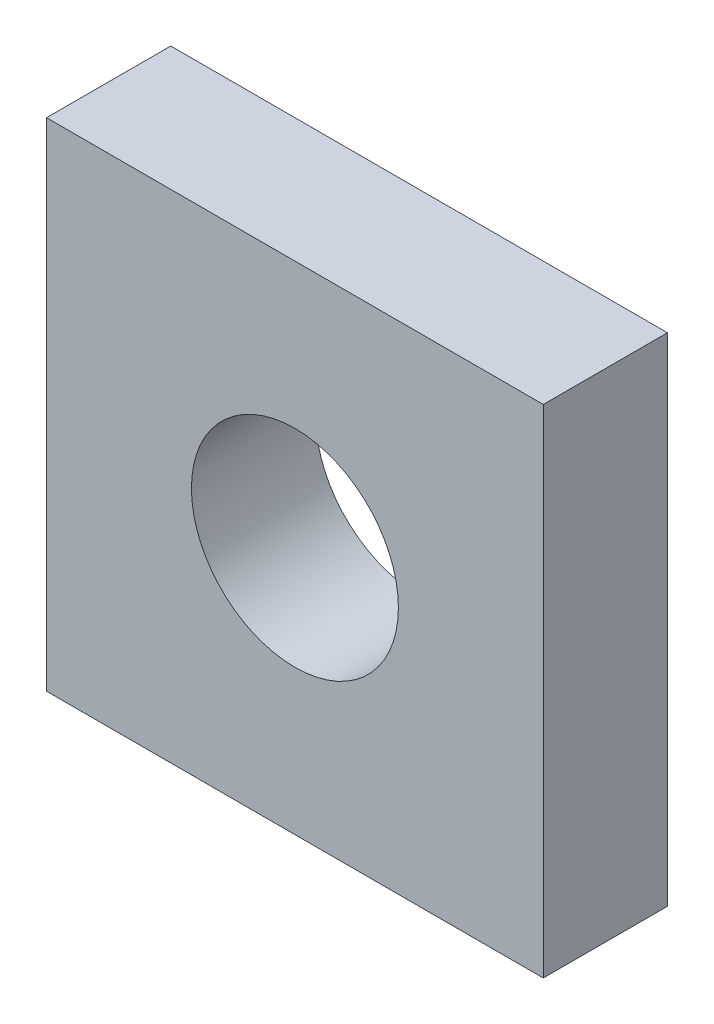
SolidWorks part; units mm, degrees
material "1.0038 (S235JRG2)"
ref_plane "Plan de face" through (0, 0, 0) normal (0, 0, 1) x (1, 0, 0)
ref_plane "Plan de dessus" through (0, 0, 0) normal (0, 1, 0) x (1, 0, 0)
ref_plane "Plan de droite" through (0, 0, 0) normal (1, 0, 0) x (0, 0, -1)
sketch "Esquisse1" plane through (0, 0, 0) normal (0, 0, 1) x (1, 0, 0)
  line L0 (-30, 0) -> (30, 0)
other "Elément mécano-soudé1"
ref_plane "Plan1" through (-30, 0, 0) normal (1, 0, 0) x (0, 1, 0)
sketch "plat" plane through (-30, 0, 0) normal (1, 0, 0) x (0, 1, 0)
  line L0 (-30, 0) -> (30, 0) construction
  line L1 (-30, 7.5) -> (30, 7.5)
  line L2 (-30, 7.5) -> (-30, -7.5)
  line L3 (-30, -7.5) -> (30, -7.5)
  line L4 (30, 7.5) -> (30, -7.5)
  line L5 (0, 7.5) -> (0, -7.5) construction
  point P8 (0, 0)
  dimension "B" = 60
  dimension "A" = 15
sketch "Esquisse2" plane through (0, 0, 7.5) normal (0, 0, 1) x (1, 0, 0)
  circle A0 centre (0, 0) radius 12.5
  dimension "D1" = 25
extrude "Enlèv. mat.-Extru.1" cut sketch "Esquisse2" against normal blind 20
